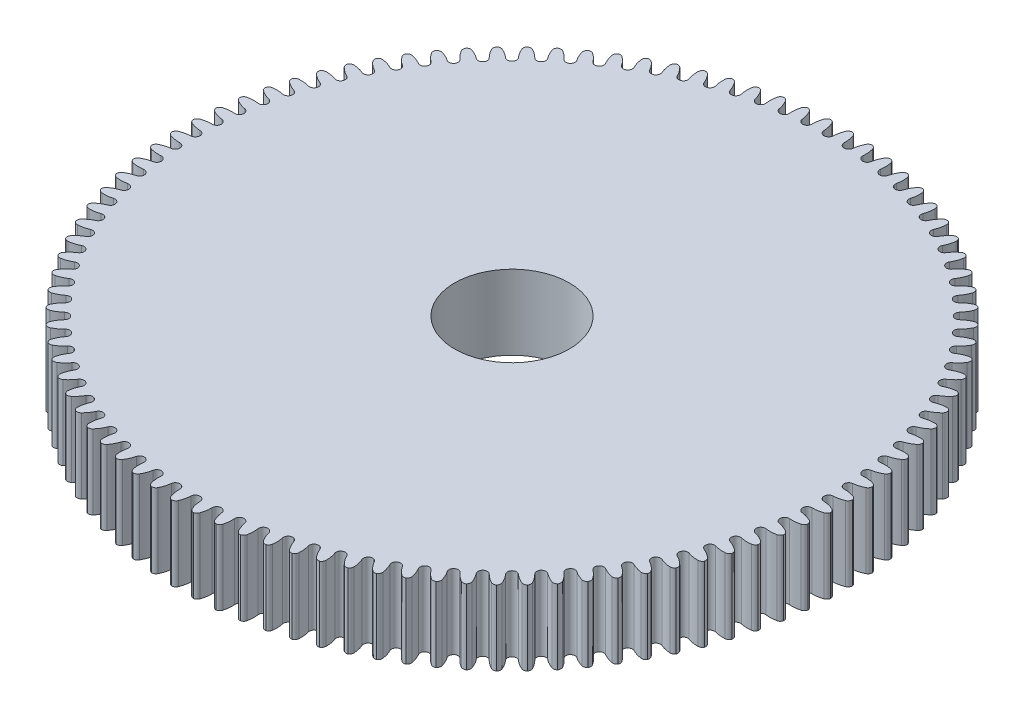
SolidWorks part; units mm, degrees
ref_plane "Front Plane" through (0, 0, 0) normal (0, 0, 1) x (1, 0, 0)
ref_plane "Top Plane" through (0, 0, 0) normal (0, 1, 0) x (1, 0, 0)
ref_plane "Right Plane" through (0, 0, 0) normal (1, 0, 0) x (0, 0, -1)
sketch "Sketch1" plane through (0, 0, 0) normal (0, 1, 0) x (1, 0, 0)
  circle A0 centre (0, 0) radius 57.5
  dimension "D1" = 115
extrude "Boss-Extrude1" add sketch "Sketch1" along normal blind 13
sketch "Sketch3" plane through (0, 0, 0) normal (0, -1, 0) x (1, 0, 0)
  line L0 (0, -55.2166) -> (0, -60.2569) construction
  arc A0 (0.7992, -55.1799) -> (-0.7992, -55.1799) centre (0, -55.2166) ccw
  arc A1 (0.7992, -55.1799) -> (1.2101, -56.9803) centre (5.9937, -54.9414) ccw
  circle A2 centre (1.946, -56.6666) radius 0.8
  circle A3 centre (0, 0) radius 57.5 construction
  circle A4 centre (-1.946, -56.6666) radius 0.8
  arc A5 (-0.7992, -55.1799) -> (-1.2101, -56.9803) centre (-5.9937, -54.9414) cw
  dimension "D1" = 1.6
  dimension "D2" = 10.4
  dimension "D3" = 1.45
  dimension "D4" = 1.6
  dimension "D5" = 3.892
extrude "Cut-Extrude1" cut sketch "Sketch3" against normal blind 13
pattern_circular "CirPattern1" count 96 over 360 about axis through (0, 0, 0) along (0, 1, 0) of "Cut-Extrude1"
sketch "Sketch4" plane through (0, 0, 0) normal (0, -1, 0) x (1, 0, 0)
  circle A0 centre (0, 0) radius 10
  dimension "D1" = 20
extrude "Cut-Extrude3" cut sketch "Sketch4" against normal blind 13
sketch "Croquis1" plane through (0, 0, 0) normal (0, -1, 0) x (1, 0, 0)
  line L0 (0, 0) -> (0, 54.4166) construction
  arc A0 (-0.7992, 55.1799) -> (0.7992, 55.1799) centre (0, 55.2166) ccw construction
